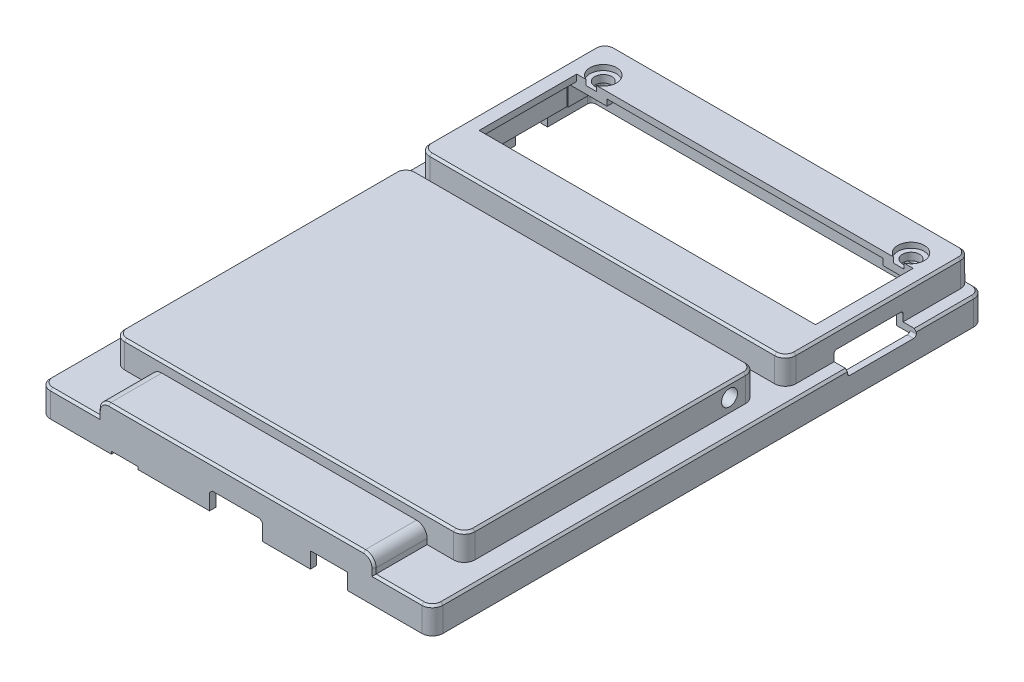
SolidWorks part; units mm, degrees
ref_plane "前视基准面" through (0, 0, 0) normal (0, 0, 1) x (1, 0, 0)
ref_plane "上视基准面" through (0, 0, 0) normal (0, 1, 0) x (1, 0, 0)
ref_plane "右视基准面" through (0, 0, 0) normal (1, 0, 0) x (0, 0, -1)
sketch "草图1" plane through (0, 0, 0) normal (0, 1, 0) x (1, 0, 0)
  line L1 (-37, 52) -> (37, 52)
  line L2 (-37, 52) -> (-37, -52)
  line L3 (-37, -52) -> (37, -52)
  line L4 (37, 52) -> (37, -52)
  line L5 (-37, 52) -> (37, -52) construction
  line L6 (-37, -52) -> (37, 52) construction
  point P0 (0, 0)
  dimension "D1" = 104
  dimension "D2" = 74
extrude "凸台-拉伸1" add sketch "草图1" along normal blind 5
sketch "草图2" plane through (0, 5, 0) normal (0, 1, 0) x (1, 0, 0)
  line L0 (-37, -52) -> (37, -52) construction
  line L1 (-26, -52) -> (26, -52)
  line L2 (-26, -52) -> (-26, 13)
  line L3 (-26, 13) -> (26, 13)
  line L4 (26, -52) -> (26, 13)
  line L5 (-37, 52) -> (-37, -52) construction
  dimension "D1" = 52
  dimension "D2" = 11
  dimension "D3" = 65
extrude "凸台-拉伸2" add sketch "草图2" along normal blind 3
sketch "草图4" plane through (0, 5, 0) normal (0, 1, 0) x (1, 0, 0)
  line L0 (37, 52) -> (-37, 52) construction
  line L1 (-34.5, 52) -> (34.5, 52)
  line L2 (-34.5, 52) -> (-34.5, 17)
  line L3 (-34.5, 17) -> (34.5, 17)
  line L4 (34.5, 52) -> (34.5, 17)
  line L5 (-37, 52) -> (-37, -52) construction
  line L6 (37, -52) -> (37, 52) construction
  dimension "D1" = 35
  dimension "D2" = 2.5
  dimension "D3" = 2.5
extrude "凸台-拉伸4" add sketch "草图4" along normal blind 5
sketch "草图5" plane through (0, 5, 0) normal (0, 1, 0) x (1, 0, 0)
  line L0 (26, 13) -> (-26, 13) construction
  line L1 (-33, 13) -> (33, 13)
  line L2 (-33, 13) -> (-33, -42)
  line L3 (-33, -42) -> (33, -42)
  line L4 (33, 13) -> (33, -42)
  line L5 (-26, 13) -> (-26, -52) construction
  line L6 (26, -52) -> (26, 13) construction
  line L7 (-26, -52) -> (26, -52) construction
  dimension "D1" = 0
  dimension "D2" = 7
  dimension "D3" = 7
  dimension "D4" = 10
extrude "凸台-拉伸5" add sketch "草图5" along normal blind 5
fillet "圆角1" radius 2 4 edges at (37, 2.5, 52) (37, 2.5, -52) (-37, 2.5, -52) (-37, 2.5, 52)
fillet "圆角2" radius 2 8 edges at (-34.5, 7.5, -52) (34.5, 7.5, -52) (34.5, 7.5, -17) (33, 7.5, -13) (33, 7.5, 42) (-33, 7.5, 42) (-33, 7.5, -13) (-34.5, 7.5, -17)
shell "抽壳2" thickness 1.2
fillet "圆角4" radius 2 2 edges at (26, 8, 47) (-26, 8, 47)
fillet "圆角5" radius 1 2 edges at (24.8, 6.8, 45.8) (-24.8, 6.8, 45.8)
sketch "草图6" plane through (0, 10, 0) normal (0, 1, 0) x (1, 0, 0)
  line L0 (32.5, 52) -> (-32.5, 52) construction
  line L1 (-31.7, 43.9) -> (31.7, 43.9)
  line L2 (-31.7, 43.9) -> (-31.7, 25.5)
  line L3 (-31.7, 25.5) -> (31.7, 25.5)
  line L4 (31.7, 43.9) -> (31.7, 25.5)
  line L5 (-32.5, 17) -> (32.5, 17) construction
  line L6 (-34.5, 50) -> (-34.5, 19) construction
  line L7 (34.5, 19) -> (34.5, 50) construction
  dimension "D1" = 8.1
  dimension "D2" = 8.5
  dimension "D3" = 2.8
  dimension "D4" = 2.8
extrude "切除-拉伸1" cut sketch "草图6" against normal blind 10
sketch "草图7" plane through (0, 3.8, 0) normal (0, -1, 0) x (1, 0, 0)
  line L0 (-31.7, -25.5) -> (31.7, -25.5) construction
  line L1 (-33.3, -18.2) -> (-26, -18.2)
  line L2 (-33.3, -18.2) -> (-33.3, -25.5)
  line L3 (-33.3, -25.5) -> (-26, -25.5)
  line L4 (-26, -18.2) -> (-26, -25.5)
  line L5 (35, -50.8) -> (-35, -50.8) construction
  line L6 (-33.3, -50.8) -> (-26, -50.8)
  line L7 (-33.3, -50.8) -> (-33.3, -43.9)
  line L8 (-33.3, -43.9) -> (-26, -43.9)
  line L9 (-26, -50.8) -> (-26, -43.9)
  line L10 (31.7, -43.9) -> (-31.7, -43.9) construction
  line L11 (-33.3, -50) -> (-33.3, -19) construction
  line L12 (33.3, -50.8) -> (26, -50.8)
  line L13 (33.3, -50.8) -> (33.3, -43.9)
  line L14 (33.3, -43.9) -> (26, -43.9)
  line L15 (26, -50.8) -> (26, -43.9)
  line L16 (33.3, -18.2) -> (26, -18.2)
  line L17 (33.3, -18.2) -> (33.3, -25.5)
  line L18 (33.3, -25.5) -> (26, -25.5)
  line L19 (26, -18.2) -> (26, -25.5)
  line L20 (-32.5, -18.2) -> (32.5, -18.2) construction
  line L23 (33.3, -19) -> (33.3, -50) construction
  line L25 (33.3, -19) -> (33.3, -50) construction
  point P22 (-26, -47.35)
  dimension "D1" = 7.3
  dimension "D2" = 7.3
  dimension "D3" = 0
  dimension "D4" = 7.3
  dimension "D5" = 7.3
sketch "草图8" plane through (0, 8.8, 0) normal (0, -1, 0) x (1, 0, 0)
  line L4 (-33.3, -50.8) -> (-26, -50.8)
  line L5 (-26, -50.8) -> (-26, -43.9)
  line L6 (-26, -43.9) -> (-33.3, -43.9)
  line L7 (-33.3, -43.9) -> (-33.3, -50.8)
  line L8 (-33.3, -50.8) -> (-26, -50.8)
  line L9 (-26, -50.8) -> (-26, -43.9)
  line L10 (-26, -43.9) -> (-33.3, -43.9)
  line L11 (-33.3, -43.9) -> (-33.3, -50.8)
  line L28 (26, -50.8) -> (33.3, -50.8)
  line L29 (33.3, -50.8) -> (33.3, -43.9)
  line L30 (33.3, -43.9) -> (26, -43.9)
  line L31 (26, -43.9) -> (26, -50.8)
  line L32 (26, -50.8) -> (33.3, -50.8)
  line L33 (33.3, -50.8) -> (33.3, -43.9)
  line L34 (33.3, -43.9) -> (26, -43.9)
  line L35 (26, -43.9) -> (26, -50.8)
  dimension "D1" = 0
  dimension "D4" = 0
extrude "凸台-拉伸6" add sketch "草图8" along normal blind 1.2
sketch "草图9" plane through (0, 3.8, 0) normal (0, -1, 0) x (1, 0, 0)
  line L0 (-35, 50.8) -> (35, 50.8) construction
  line L1 (-24.8, 44.3) -> (-35.8, 44.3)
  line L2 (-24.8, 44.3) -> (-24.8, 50.8)
  line L3 (-24.8, 50.8) -> (-35.8, 50.8)
  line L4 (-35.8, 44.3) -> (-35.8, 50.8)
  line L5 (24.8, 44.3) -> (35.8, 44.3)
  line L6 (24.8, 44.3) -> (24.8, 50.8)
  line L7 (24.8, 50.8) -> (35.8, 50.8)
  line L8 (35.8, 44.3) -> (35.8, 50.8)
  line L9 (-35.8, -50) -> (-35.8, 50) construction
  line L10 (35.8, 50) -> (35.8, -50) construction
  line L11 (-24.8, 40.8) -> (-24.8, 50.8) construction
  line L12 (24.8, 50.8) -> (24.8, 40.8) construction
  point P19 (30.3, 44.3)
  dimension "D1" = 6.5
  dimension "D2" = 6.5
extrude "凸台-拉伸7" add sketch "草图9" along normal up to surface (3.8 mm away) up to face at (0, 0, 0)
sketch "草图10" plane through (0, 10, 0) normal (0, 1, 0) x (1, 0, 0)
  line L0 (32.5, 52) -> (-32.5, 52) construction
  line L1 (-29, 46.2) -> (29, 46.2) construction
  line L2 (-29, 46.2) -> (-29, 23.2) construction
  line L3 (-29, 23.2) -> (29, 23.2) construction
  line L4 (29, 46.2) -> (29, 23.2) construction
  line L6 (34.5, 19) -> (34.5, 50) construction
  line L7 (-34.5, 50) -> (-34.5, 19) construction
  line L8 (-32.5, 17) -> (32.5, 17) construction
  circle A0 centre (-29, 46.2) radius 1.6
  circle A1 centre (29, 46.2) radius 1.6
  dimension "D5" = 3.2
  dimension "D6" = 3.2
  dimension "D1" = 5.8
  dimension "D2" = 6.2
  dimension "D3" = 5.5
  dimension "D4" = 5.5
extrude "切除-拉伸2" cut sketch "草图10" against normal blind 13
sketch "草图12" plane through (0, 0, 0) normal (0, -1, 0) x (1, 0, 0)
  line L0 (-37, -50) -> (-37, 50) construction
  line L1 (-35, 52) -> (35, 52) construction
  line L2 (37, 50) -> (37, -50) construction
  circle A0 centre (-29, 48) radius 1.5
  circle A1 centre (29, 48) radius 1.5
  dimension "D3" = 3
  dimension "D6" = 3
  dimension "D1" = 8
  dimension "D2" = 4
  dimension "D4" = 4
  dimension "D5" = 8
extrude "切除-拉伸4" cut sketch "草图12" against normal blind 3.5
sketch "草图13" plane through (0, 10, 0) normal (0, 1, 0) x (1, 0, 0)
  circle A0 centre (-29, 46.2) radius 2.5
  circle A1 centre (29, 46.2) radius 2.5
  dimension "D1" = 5
  dimension "D4" = 5
extrude "切除-拉伸5" cut sketch "草图13" against normal blind 1
sketch "草图14" plane through (0, 3.8, 0) normal (0, -1, 0) x (1, 0, 0)
  line L1 (-31.8, -4.8) -> (-28, -4.8)
  line L2 (-31.8, -4.8) -> (-31.8, -11.8)
  line L3 (-31.8, -11.8) -> (-28, -11.8)
  line L4 (-28, -4.8) -> (-28, -11.8)
  line L5 (31, -11.8) -> (-31, -11.8) construction
  line L6 (31, -11.8) -> (-31, -11.8) construction
  line L7 (28, -11.8) -> (31.8, -11.8)
  line L8 (28, -11.8) -> (28, -4.8)
  line L9 (28, -4.8) -> (31.8, -4.8)
  line L10 (31.8, -11.8) -> (31.8, -4.8)
  line L12 (31.8, 40) -> (31.8, -11) construction
  line L13 (-31.8, -11) -> (-31.8, 40) construction
  line L14 (-37, -50) -> (-37, 50) construction
  line L15 (37, 50) -> (37, -50) construction
  dimension "D1" = 7
  dimension "D2" = 7
  dimension "D3" = 9
  dimension "D4" = 9
extrude "凸台-拉伸8" add sketch "草图14" against normal blind 5
fillet "圆角6" radius 1 6 edges at (28, 6.3, -11.8) (31.8, 6.3, -4.8) (28, 6.3, -4.8) (-28, 6.3, -11.8) (-28, 6.3, -4.8) (-31.8, 6.3, -4.8)
sketch "草图15" plane through (0, 0, -52) normal (0, 0, -1) x (-1, 0, 0)
  line L0 (37, 5) -> (37, 0) construction
  line L1 (17, 7.8) -> (26, 7.8)
  line L2 (17, 7.8) -> (17, 3.8)
  line L3 (17, 3.8) -> (26, 3.8)
  line L4 (26, 7.8) -> (26, 3.8)
  line L5 (4.5, 7.8) -> (13.5, 7.8)
  line L6 (4.5, 7.8) -> (4.5, 3.8)
  line L7 (4.5, 3.8) -> (13.5, 3.8)
  line L8 (13.5, 7.8) -> (13.5, 3.8)
  line L9 (-26.5, 8.8) -> (-13.5, 8.8)
  line L10 (-26.5, 8.8) -> (-26.5, 3.8)
  line L11 (-26.5, 3.8) -> (-13.5, 3.8)
  line L12 (-13.5, 8.8) -> (-13.5, 3.8)
  line L13 (-32.5, 10) -> (32.5, 10) construction
  line L14 (-37, 0) -> (-37, 5) construction
  dimension "D1" = 11
  dimension "D2" = 9
  dimension "D3" = 3.5
  dimension "D4" = 9
  dimension "D5" = 2.2
  dimension "D6" = 4
  dimension "D7" = 2.2
  dimension "D8" = 4
  dimension "D9" = 10.5
  dimension "D10" = 13
  dimension "D11" = 1.2
  dimension "D12" = 5
extrude "切除-拉伸6" cut sketch "草图15" against normal blind 5
fillet "圆角7" radius 2 6 edges at (13.5, 3.8, -51.4) (26.5, 3.8, -51.4) (-4.5, 3.8, -51.4) (-13.5, 3.8, -51.4) (-17, 3.8, -51.4) (-26, 3.8, -51.4)
sketch "草图16" plane through (-37, 0, 0) normal (-1, 0, 0) x (0, 0, 1)
  line L0 (-50, 0) -> (50, 0) construction
  line L1 (-42.5, 0) -> (-36.5, 0)
  line L2 (-42.5, 0) -> (-42.5, 2)
  line L3 (-42.5, 2) -> (-36.5, 2)
  line L4 (-36.5, 0) -> (-36.5, 2)
  line L5 (-52, 0) -> (-52, 5) construction
  point P8 (-42.5, 1)
  dimension "D1" = 9.5
  dimension "D2" = 6
  dimension "D3" = 2
extrude "切除-拉伸7" cut sketch "草图16" against normal blind 5
sketch "草图17" plane through (0, 0, 52) normal (0, 0, 1) x (1, 0, 0)
  line L0 (-35, 0) -> (35, 0) construction
  line L1 (21, 0) -> (14, 0)
  line L2 (21, 0) -> (21, 2)
  line L3 (21, 2) -> (14, 2)
  line L4 (14, 0) -> (14, 2)
  line L5 (-37, 0) -> (-37, 5) construction
  line L6 (5, 0) -> (-5, 0)
  line L7 (5, 0) -> (5, 3.5)
  line L8 (5, 3.5) -> (-5, 3.5)
  line L9 (-5, 0) -> (-5, 3.5)
  line L10 (-18.5, 0) -> (-23.5, 0)
  line L11 (-18.5, 0) -> (-18.5, 0.5)
  line L12 (-18.5, 0.5) -> (-23.5, 0.5)
  line L13 (-23.5, 0) -> (-23.5, 0.5)
  dimension "D1" = 13.5
  dimension "D2" = 5
  dimension "D3" = 0.5
  dimension "D4" = 13.5
  dimension "D5" = 10
  dimension "D6" = 3.5
  dimension "D7" = 2
  dimension "D8" = 9
  dimension "D9" = 7
extrude "切除-拉伸8" cut sketch "草图17" against normal blind 5
chamfer "倒角1" distance 0.5 angle 45 2 edges at (-5, 3.5, 51.4) (5, 3.5, 51.4)
sketch "草图18" plane through (-33, 0, 0) normal (-1, 0, 0) x (0, 0, 1)
  line L0 (-11, 10) -> (40, 10) construction
  line L1 (-13, 5) -> (-13, 10) construction
  circle A0 centre (-8, 7.5) radius 1.5
  dimension "D2" = 3
  dimension "D1" = 2.5
  dimension "D3" = 5
extrude "切除-拉伸9" cut sketch "草图18" against normal blind 3.5
sketch "草图19" plane through (33, 0, 0) normal (1, 0, 0) x (0, 0, -1)
  line L0 (-40, 10) -> (11, 10) construction
  line L1 (13, 10) -> (13, 5) construction
  circle A0 centre (8, 7.5) radius 1.5
  dimension "D2" = 3
  dimension "D1" = 2.5
  dimension "D3" = 5
extrude "切除-拉伸10" cut sketch "草图19" against normal blind 3.5
sketch "草图20" plane through (-33.3, 0, 0) normal (1, 0, 0) x (0, 0, -1)
  line L0 (50, 3.8) -> (19, 3.8) construction
  line L1 (25.5, 8.8) -> (43.9, 8.8)
  line L2 (25.5, 8.8) -> (25.5, 3.8)
  line L3 (25.5, 3.8) -> (43.9, 3.8)
  line L4 (43.9, 8.8) -> (43.9, 3.8)
  line L5 (43.9, 7.6) -> (43.9, 8.8) construction
  line L6 (43.9, 8.8) -> (19, 8.8) construction
  dimension "D1" = 0
  dimension "D2" = 18.4
extrude "切除-拉伸11" cut sketch "草图20" against normal blind 0.2
chamfer "倒角2" distance 0.4 angle 45 31 edges at (30.5, 5, 52) (33.75, 5, -52) (36.4142, 5, 51.4142) (36.4142, 5, -51.4142) (37, 5, 0) (-33.75, 5, -52) (-30.5, 5, 52) (-36.4142, 5, -51.4142) (-36.4142, 5, 51.4142) (-37, 5, 0) (33, 10, 14.5) (32.4142, 10, -12.4142) (32.4142, 10, 41.4142) (0, 10, -13) (0, 10, 42) (-32.4142, 10, -12.4142) (-32.4142, 10, 41.4142) (-33, 10, 14.5) (34.5, 10, -34.5) (33.9142, 10, -51.4142) (33.9142, 10, -17.5858) (0, 10, -52) (0, 10, -17) (-33.9142, 10, -51.4142) (-33.9142, 10, -17.5858) (-34.5, 10, -34.5) (26, 5.5, 52) (25.4142, 7.4142, 52) (0, 8, 52) (-25.4142, 7.4142, 52) (-26, 5.5, 52)
sketch "草图21" plane through (33.3, 0, 0) normal (-1, 0, 0) x (0, 0, 1)
  line L1 (-39.2, 3.8) -> (-26.2, 3.8)
  line L2 (-39.2, 3.8) -> (-39.2, 6.8)
  line L3 (-39.2, 6.8) -> (-26.2, 6.8)
  line L4 (-26.2, 3.8) -> (-26.2, 6.8)
  line L5 (-18.2, 3.8) -> (-18.2, 8.8) construction
  line L6 (-19, 3.8) -> (-50, 3.8) construction
  dimension "D1" = 3
  dimension "D2" = 13
  dimension "D3" = 8
  dimension "D4" = 0
extrude "切除-拉伸12" cut sketch "草图21" against normal blind 10
fillet "圆角8" radius 0.5 4 edges at (36.4, 3.8, -39.2) (36.4, 3.8, -26.2) (33.9, 6.8, -39.2) (33.9, 6.8, -26.2)
chamfer "倒角5" distance 1 angle 45 1 edges at (17.5, 2, 52)
